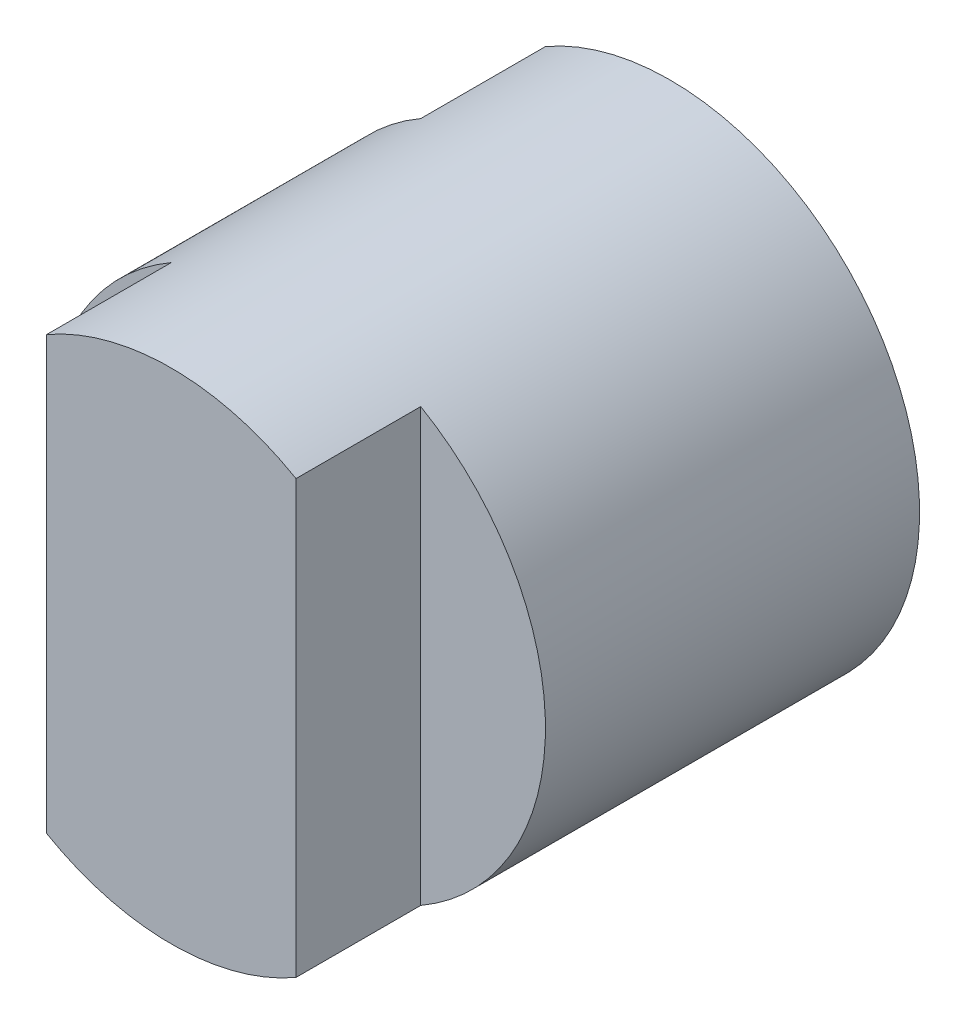
SolidWorks part; units mm, degrees
ref_plane "Front" through (0, 0, 0) normal (0, 0, 1) x (1, 0, 0)
ref_plane "Top" through (0, 0, 0) normal (0, 1, 0) x (1, 0, 0)
ref_plane "Right" through (0, 0, 0) normal (1, 0, 0) x (0, 0, -1)
sketch "Sketch1" plane through (0, 0, 0) normal (0, 0, 1) x (1, 0, 0)
  circle A0 centre (0, 0) radius 2
  dimension "D1" = 4
extrude "Boss-Extrude1" add sketch "Sketch1" along normal blind 4
sketch "Sketch2" plane through (0, 0, 0) normal (0, 1, 0) x (1, 0, 0)
  line L0 (2, -3) -> (1, -3)
  line L1 (2, -4) -> (2, 0) construction
  line L2 (1, -3) -> (1, -4.2215)
  line L3 (1, -4.2215) -> (-1, -4.2646)
  line L4 (-1, -4.2646) -> (-1, -3)
  line L5 (-1, -3) -> (-2.3139, -3)
  line L6 (-2.3139, -3) -> (-2.3139, -1)
  line L7 (-2.3139, -1) -> (-1, -1)
  line L8 (-1, -1) -> (-1, 0.234)
  line L9 (-1, 0.234) -> (-2.5868, 0.1999)
  line L10 (-2.5868, 0.1999) -> (-2.4898, -4.307)
  line L11 (-2.4898, -4.307) -> (2, -4.619)
  line L12 (2, -4.619) -> (2.5546, -4.2215)
  line L13 (2.5546, -4.2215) -> (2, -3)
  line L14 (-2, -4) -> (2, -4) construction
  line L15 (-2, 0) -> (-2, -4) construction
  line L16 (2, 0) -> (-2, 0) construction
  dimension "D1" = 1
  dimension "D2" = 1
  dimension "D3" = 1.2215
  dimension "D4" = 1
  dimension "D5" = 1
  dimension "D6" = 1
  dimension "D7" = 1
extrude "Cut-Extrude1" cut sketch "Sketch2" against normal mid plane 10
